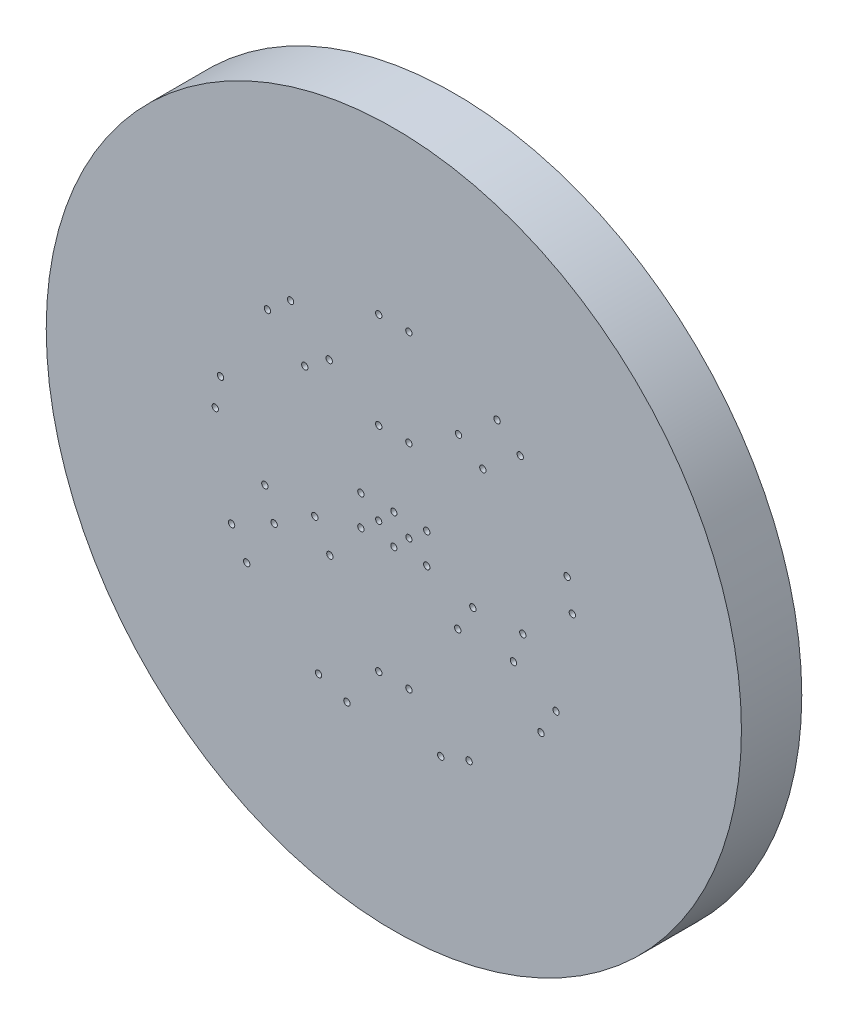
SolidWorks part; units mm, degrees
material "Nichel"
ref_plane "Piano frontale" through (0, 0, 0) normal (0, 0, 1) x (1, 0, 0)
ref_plane "Piano superiore" through (0, 0, 0) normal (0, 1, 0) x (1, 0, 0)
ref_plane "Piano destro" through (0, 0, 0) normal (1, 0, 0) x (0, 0, -1)
sketch "Schizzo1" plane through (0, 0, 0) normal (0, 0, 1) x (1, 0, 0)
  circle A0 centre (0, 0) radius 28.8
  dimension "D1" = 57.6
extrude "Estrusione-Estrusione1" add sketch "Schizzo1" along normal blind 5
sketch "Schizzo2" plane through (0, 0, 5) normal (0, 0, 1) x (1, 0, 0)
  line L0 (1.25, 14.7973) -> (-1.25, 14.7973) construction
  circle A0 centre (0, 0) radius 18.8 construction
  circle A1 centre (0, 0) radius 28.8 construction
  circle A2 centre (0, 0) radius 14.85 construction
  circle A3 centre (-1.25, 14.7973) radius 0.2635
  circle A4 centre (1.25, 14.7973) radius 0.2635
  dimension "D1" = 10
  dimension "D2" = 29.7
  dimension "D3" = 0.527
  dimension "D4" = 2.5
extrude "Taglio-Estrusione1" cut sketch "Schizzo2" against normal through all
pattern_circular "RipetizioneCircolare1" count 9 every 40 about axis through (0, -0.0025, 0) along (0, 0, 1) of "Taglio-Estrusione1"
sketch "Schizzo6" plane through (0, 0, 5) normal (0, 0, 1) x (1, 0, 0)
  line L1 (-1.25, -10.8281) -> (1.25, -10.8281) construction
  circle A0 centre (0, 0) radius 10.9 construction
  circle A3 centre (-1.25, -10.8281) radius 0.2635
  circle A4 centre (1.25, -10.8281) radius 0.2635
  dimension "D1" = 21.8
  dimension "D5" = 0.527
  dimension "D4" = 2.5
extrude "Taglio-Estrusione2" cut sketch "Schizzo6" against normal through all
pattern_circular "RipetizioneCircolare2" count 5 every 72 about axis through (0, 0.0018, 0) along (0, 0, 1) of "Taglio-Estrusione2"
sketch "Schizzo7" plane through (0, 0, 5) normal (0, 0, 1) x (1, 0, 0)
  line L0 (-1.25, 6.8367) -> (1.25, 6.8367) construction
  circle A0 centre (0, 0) radius 6.95 construction
  circle A1 centre (-1.25, 6.8367) radius 0.2635
  circle A2 centre (1.25, 6.8367) radius 0.2635
  dimension "D1" = 13.9
  dimension "D2" = 0.527
  dimension "D3" = 2.5
extrude "Taglio-Estrusione3" cut sketch "Schizzo7" against normal through all
pattern_circular "RipetizioneCircolare3" count 3 every 120 about axis through (0, -0.0011, 0) along (0, 0, 1) of "Taglio-Estrusione3"
sketch "Schizzo8" plane through (0, 0, 5) normal (0, 0, 1) x (1, 0, 0)
  line L1 (2.7272, -1.25) -> (2.7272, 1.25) construction
  circle A0 centre (0, 0) radius 3 construction
  circle A3 centre (2.7272, 1.25) radius 0.2635
  circle A4 centre (2.7272, -1.25) radius 0.2635
  dimension "D1" = 6
  dimension "D5" = 0.527
  dimension "D4" = 2.5
extrude "Taglio-Estrusione4" cut sketch "Schizzo8" against normal through all
pattern_circular "RipetizioneCircolare4" count 2 every 180 about axis through (-0.0005, 0, 0) along (0, 0, 1) of "Taglio-Estrusione4"
sketch "Schizzo9" plane through (0, 0, 5) normal (0, 0, 1) x (1, 0, 0)
  line L0 (-1.25, 0) -> (1.25, 0) construction
  line L2 (0, 1.25) -> (0, -1.25) construction
  circle A0 centre (0, 0) radius 1.25 construction
  circle A1 centre (-1.25, 0) radius 0.2545
  circle A2 centre (1.25, 0) radius 0.2545
  circle A3 centre (0, -1.25) radius 0.2545
  circle A4 centre (0, 1.25) radius 0.2545
  dimension "D1" = 2.5
  dimension "D4" = 0.509
  dimension "D2" = 2.5
  dimension "D3" = 2.5
extrude "Taglio-Estrusione5" cut sketch "Schizzo9" against normal through all
